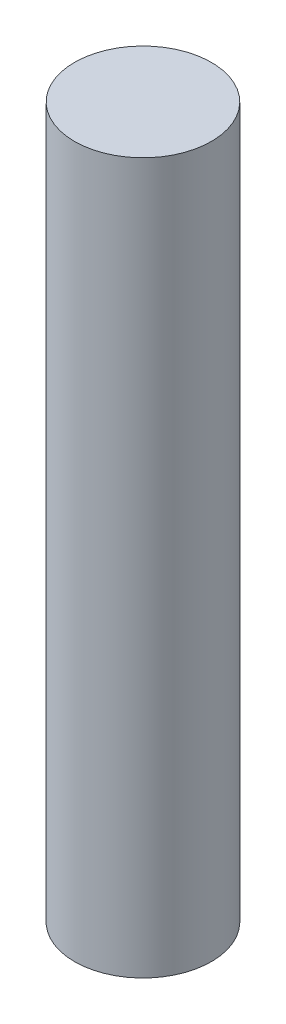
SolidWorks part; units mm, degrees
ref_plane "Front Plane" through (0, 0, 0) normal (0, 0, 1) x (1, 0, 0)
ref_plane "Top Plane" through (0, 0, 0) normal (0, 1, 0) x (1, 0, 0)
ref_plane "Right Plane" through (0, 0, 0) normal (1, 0, 0) x (0, 0, -1)
sketch "Sketch1" plane through (0, 0, 0) normal (0, 1, 0) x (1, 0, 0)
  circle A0 centre (0, 0) radius 4
  dimension "D1" = 8
extrude "Extrude1" add sketch "Sketch1" against normal blind 41.5
